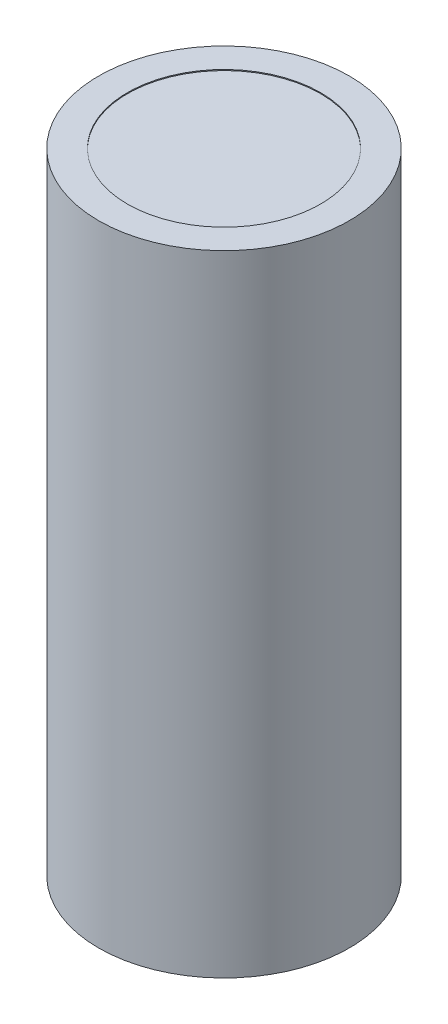
SolidWorks part; units mm, degrees
ref_plane "Plan de face" through (0, 0, 0) normal (0, 0, 1) x (1, 0, 0)
ref_plane "Plan de dessus" through (0, 0, 0) normal (0, 1, 0) x (1, 0, 0)
ref_plane "Plan de droite" through (0, 0, 0) normal (1, 0, 0) x (0, 0, -1)
sketch "Esquisse1" plane through (0, 0, 0) normal (0, 1, 0) x (1, 0, 0)
  circle A0 centre (0, 0) radius 13.075
  dimension "D1" = 26.15
extrude "Boss.-Extru.1" add sketch "Esquisse1" along normal blind 65.7
sketch "Esquisse2" plane through (0, 65.7, 0) normal (0, 1, 0) x (1, 0, 0)
  circle A0 centre (0, 0) radius 10.075
  circle A1 centre (0, 0) radius 13.075 construction
  dimension "D1" = 3
extrude "Enlèv. mat.-Extru.1" cut sketch "Esquisse2" against normal blind 0.1
sketch "Esquisse3" plane through (0, 0, 0) normal (0, -1, 0) x (1, 0, 0)
  circle A0 centre (0, 0) radius 7.075
  circle A1 centre (0, 0) radius 8.575
  circle A2 centre (0, 0) radius 13.075 construction
  dimension "D1" = 4.5
  dimension "D2" = 1.5
extrude "Enlèv. mat.-Extru.2" cut sketch "Esquisse3" against normal blind 2
